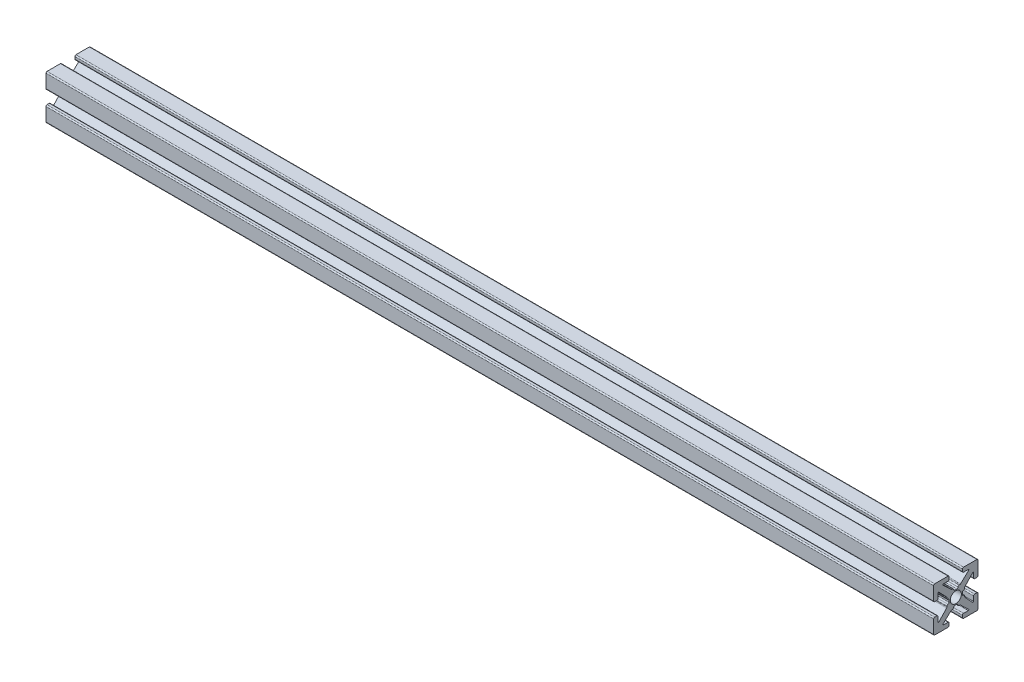
SolidWorks part; units mm, degrees
material "1060 Сплав"
ref_plane "Front Plane" through (0, 0, 0) normal (0, 0, 1) x (1, 0, 0)
ref_plane "Top Plane" through (0, 0, 0) normal (0, 1, 0) x (1, 0, 0)
ref_plane "Right Plane" through (0, 0, 0) normal (1, 0, 0) x (0, 0, -1)
sketch "Sketch1" plane through (0, 0, 0) normal (1, 0, 0) x (0, 0, -1)
  line L0 (0, 0) -> (0, 1.4948) construction
  line L1 (-0.2413, 1.4948) -> (0.2413, 1.4948)
  line L2 (5, 1.7526) -> (5, 4.746)
  line L3 (0.7493, 2.0028) -> (0.8899, 2.0028)
  line L4 (1.0639, 2.0718) -> (2.8908, 3.7899)
  line L5 (2.8038, 4.0094) -> (1.7526, 4.0094)
  line L6 (1.4986, 4.2634) -> (1.4986, 4.746)
  line L7 (1.7526, 5) -> (4.746, 5)
  line L8 (5, 5) -> (0, 0) construction
  line L9 (0, 0) -> (8.6271, 0) construction
  line L10 (0, 0) -> (0, 5) construction
  line L11 (4.2634, 1.4986) -> (4.746, 1.4986)
  line L12 (4.0094, 2.8038) -> (4.0094, 1.7526)
  line L13 (2.0718, 1.0639) -> (3.7899, 2.8908)
  line L14 (2.0028, 0.7493) -> (2.0028, 0.8899)
  line L15 (1.4948, -0.2413) -> (1.4948, 0.2413)
  line L16 (0, 0) -> (1.4948, 0) construction
  line L17 (-0.2413, -1.4948) -> (0.2413, -1.4948)
  line L18 (0.7493, -2.0028) -> (0.8899, -2.0028)
  line L19 (1.0639, -2.0718) -> (2.8908, -3.7899)
  line L20 (2.8038, -4.0094) -> (1.7526, -4.0094)
  line L21 (1.4986, -4.2634) -> (1.4986, -4.746)
  line L22 (1.7526, -5) -> (4.746, -5)
  line L23 (5, -1.7526) -> (5, -4.746)
  line L24 (4.2634, -1.4986) -> (4.746, -1.4986)
  line L25 (4.0094, -2.8038) -> (4.0094, -1.7526)
  line L26 (2.0718, -1.0639) -> (3.7899, -2.8908)
  line L27 (2.0028, -0.7493) -> (2.0028, -0.8899)
  line L28 (-0.7493, 2.0028) -> (-0.8899, 2.0028)
  line L29 (-1.0639, 2.0718) -> (-2.8908, 3.7899)
  line L30 (-2.8038, 4.0094) -> (-1.7526, 4.0094)
  line L31 (-1.4986, 4.2634) -> (-1.4986, 4.746)
  line L32 (-1.7526, 5) -> (-4.746, 5)
  line L33 (-5, 1.7526) -> (-5, 4.746)
  line L34 (-4.2634, 1.4986) -> (-4.746, 1.4986)
  line L35 (-4.0094, 2.8038) -> (-4.0094, 1.7526)
  line L36 (-2.0718, 1.0639) -> (-3.7899, 2.8908)
  line L37 (-2.0028, 0.7493) -> (-2.0028, 0.8899)
  line L38 (-1.4948, -0.2413) -> (-1.4948, 0.2413)
  line L39 (-2.0028, -0.7493) -> (-2.0028, -0.8899)
  line L40 (-2.0718, -1.0639) -> (-3.7899, -2.8908)
  line L41 (-4.0094, -2.8038) -> (-4.0094, -1.7526)
  line L42 (-4.2634, -1.4986) -> (-4.746, -1.4986)
  line L43 (-5, -1.7526) -> (-5, -4.746)
  line L44 (-1.7526, -5) -> (-4.746, -5)
  line L45 (-1.4986, -4.2634) -> (-1.4986, -4.746)
  line L46 (-2.8038, -4.0094) -> (-1.7526, -4.0094)
  line L47 (-1.0639, -2.0718) -> (-2.8908, -3.7899)
  line L48 (-0.7493, -2.0028) -> (-0.8899, -2.0028)
  arc A0 (2.8908, 3.7899) -> (2.8038, 4.0094) centre (2.8038, 3.8824) ccw
  arc A1 (0.4953, 1.7488) -> (0.7493, 2.0028) centre (0.7493, 1.7488) cw
  arc A2 (0.8899, 2.0028) -> (1.0639, 2.0718) centre (0.8899, 2.2568) ccw
  arc A3 (1.7526, 4.0094) -> (1.4986, 4.2634) centre (1.7526, 4.2634) cw
  arc A4 (1.4986, 4.746) -> (1.7526, 5) centre (1.7526, 4.746) cw
  arc A5 (0.2413, 1.4948) -> (0.4953, 1.7488) centre (0.2413, 1.7488) ccw
  arc A6 (4.746, 1.4986) -> (5, 1.7526) centre (4.746, 1.7526) ccw
  arc A7 (4.0094, 1.7526) -> (4.2634, 1.4986) centre (4.2634, 1.7526) ccw
  arc A8 (3.7899, 2.8908) -> (4.0094, 2.8038) centre (3.8824, 2.8038) cw
  arc A9 (2.0028, 0.8899) -> (2.0718, 1.0639) centre (2.2568, 0.8899) cw
  arc A10 (1.7488, 0.4953) -> (2.0028, 0.7493) centre (1.7488, 0.7493) ccw
  arc A11 (1.4948, 0.2413) -> (1.7488, 0.4953) centre (1.7488, 0.2413) cw
  arc A12 (0.2413, -1.4948) -> (0.4953, -1.7488) centre (0.2413, -1.7488) cw
  arc A13 (0.4953, -1.7488) -> (0.7493, -2.0028) centre (0.7493, -1.7488) ccw
  arc A14 (0.8899, -2.0028) -> (1.0639, -2.0718) centre (0.8899, -2.2568) cw
  arc A15 (2.8908, -3.7899) -> (2.8038, -4.0094) centre (2.8038, -3.8824) cw
  arc A16 (1.7526, -4.0094) -> (1.4986, -4.2634) centre (1.7526, -4.2634) ccw
  arc A17 (1.4986, -4.746) -> (1.7526, -5) centre (1.7526, -4.746) ccw
  arc A18 (4.746, -1.4986) -> (5, -1.7526) centre (4.746, -1.7526) cw
  arc A19 (4.0094, -1.7526) -> (4.2634, -1.4986) centre (4.2634, -1.7526) cw
  arc A20 (3.7899, -2.8908) -> (4.0094, -2.8038) centre (3.8824, -2.8038) ccw
  arc A21 (2.0028, -0.8899) -> (2.0718, -1.0639) centre (2.2568, -0.8899) ccw
  arc A22 (1.7488, -0.4953) -> (2.0028, -0.7493) centre (1.7488, -0.7493) cw
  arc A23 (1.4948, -0.2413) -> (1.7488, -0.4953) centre (1.7488, -0.2413) ccw
  arc A24 (-0.2413, 1.4948) -> (-0.4953, 1.7488) centre (-0.2413, 1.7488) cw
  arc A25 (-0.4953, 1.7488) -> (-0.7493, 2.0028) centre (-0.7493, 1.7488) ccw
  arc A26 (-0.8899, 2.0028) -> (-1.0639, 2.0718) centre (-0.8899, 2.2568) cw
  arc A27 (-2.8908, 3.7899) -> (-2.8038, 4.0094) centre (-2.8038, 3.8824) cw
  arc A28 (-1.7526, 4.0094) -> (-1.4986, 4.2634) centre (-1.7526, 4.2634) ccw
  arc A29 (-1.4986, 4.746) -> (-1.7526, 5) centre (-1.7526, 4.746) ccw
  arc A30 (-4.746, 1.4986) -> (-5, 1.7526) centre (-4.746, 1.7526) cw
  arc A31 (-4.0094, 1.7526) -> (-4.2634, 1.4986) centre (-4.2634, 1.7526) cw
  arc A32 (-3.7899, 2.8908) -> (-4.0094, 2.8038) centre (-3.8824, 2.8038) ccw
  arc A33 (-2.0028, 0.8899) -> (-2.0718, 1.0639) centre (-2.2568, 0.8899) ccw
  arc A34 (-1.7488, 0.4953) -> (-2.0028, 0.7493) centre (-1.7488, 0.7493) cw
  arc A35 (-1.4948, 0.2413) -> (-1.7488, 0.4953) centre (-1.7488, 0.2413) ccw
  arc A36 (-1.4948, -0.2413) -> (-1.7488, -0.4953) centre (-1.7488, -0.2413) cw
  arc A37 (-1.7488, -0.4953) -> (-2.0028, -0.7493) centre (-1.7488, -0.7493) ccw
  arc A38 (-2.0028, -0.8899) -> (-2.0718, -1.0639) centre (-2.2568, -0.8899) cw
  arc A39 (-3.7899, -2.8908) -> (-4.0094, -2.8038) centre (-3.8824, -2.8038) cw
  arc A40 (-4.0094, -1.7526) -> (-4.2634, -1.4986) centre (-4.2634, -1.7526) ccw
  arc A41 (-4.746, -1.4986) -> (-5, -1.7526) centre (-4.746, -1.7526) ccw
  arc A42 (-1.4986, -4.746) -> (-1.7526, -5) centre (-1.7526, -4.746) cw
  arc A43 (-1.7526, -4.0094) -> (-1.4986, -4.2634) centre (-1.7526, -4.2634) cw
  arc A44 (-2.8908, -3.7899) -> (-2.8038, -4.0094) centre (-2.8038, -3.8824) ccw
  arc A45 (-0.8899, -2.0028) -> (-1.0639, -2.0718) centre (-0.8899, -2.2568) ccw
  arc A46 (-0.4953, -1.7488) -> (-0.7493, -2.0028) centre (-0.7493, -1.7488) cw
  arc A47 (-0.2413, -1.4948) -> (-0.4953, -1.7488) centre (-0.2413, -1.7488) ccw
  arc A48 (-4.746, 5) -> (-5, 4.746) centre (-4.746, 4.746) ccw
  arc A49 (-5, -4.746) -> (-4.746, -5) centre (-4.746, -4.746) ccw
  arc A50 (4.746, -5) -> (5, -4.746) centre (4.746, -4.746) ccw
  arc A51 (4.746, 5) -> (5, 4.746) centre (4.746, 4.746) cw
  point P14 (3.1242, 4.0094)
  point P19 (0.9906, 2.0028)
  point P150 (0, -1.4948)
  point P152 (-5, 5)
  point P155 (-5, -5)
  point P158 (5, -5)
  dimension "D10" = 0.127
  dimension "D11" = 0.254
  dimension "D2" = 0.254
  dimension "D1" = 10
  dimension "D3" = 2.9972
  dimension "D4" = 0.508
  dimension "D5" = 2.9972
  dimension "D6" = 0.9906
  dimension "D7" = 1.6256
  dimension "D8" = 1.9812
  dimension "D9" = 0.9906
extrude "Estrusione-Estrusione1" add sketch "Sketch1" along normal blind 200 contours L36 A32 L35 A31 L34 A30 L33 A48 L32 A29 L31 A28 L30 A27 L29 A26 L28 A25 A24 L1 A5 A1 L3 A2 L4 A0 L5 A3 L6 A4 L7 A51 L2 A6 L11 A7 L12 A8 L13 A9 L14 A10 A11 L15 A23 A22 L27 A21 L26 A20 L25 A19 L24 A18 L23 A50 L22 A17 L21 A16 L20 A15 L19 A14 L18 A13 A12 L17 A47 A46 L48 A45 L47 A44 L46 A43 L45 A42 L44 A49 L43 A41 L42 A40 L41 A39 L40 A38 L39 A37 A36 L38 A35 A34 L37 A33
hole_wizard "Foro filettato M3x0.5-1" positions "Schizzo2" profile "Schizzo1" tap size "M3x0.5" standard "Ansi Metric" end condition through all
sketch "Schizzo2" plane through (0, 0, 0) normal (-1, 0, 0) x (0, 0, 1)
  point P0 (0, 0)
sketch "Schizzo1" plane through (0, 0, 0) normal (0, 1, 0) x (0, 0, 1)
  line L0 (0, 0) -> (0, 200)
  line L1 (0, 200) -> (1.25, 200)
  line L2 (1.25, 200) -> (1.25, 0)
  line L5 (1.25, 0) -> (0, 0)
  line L11 (0, -6.35) -> (0, 107.95) construction
  dimension "Thread Major Dia." = 2.5
  dimension "Thru Tap Drill Depth" = 200
equation "\"camera plate width\"=220"
equation "\"camera plate length\"=220"
equation "\"D1@Estrusione-Estrusione1\"=\"camera plate length\" - 20"
